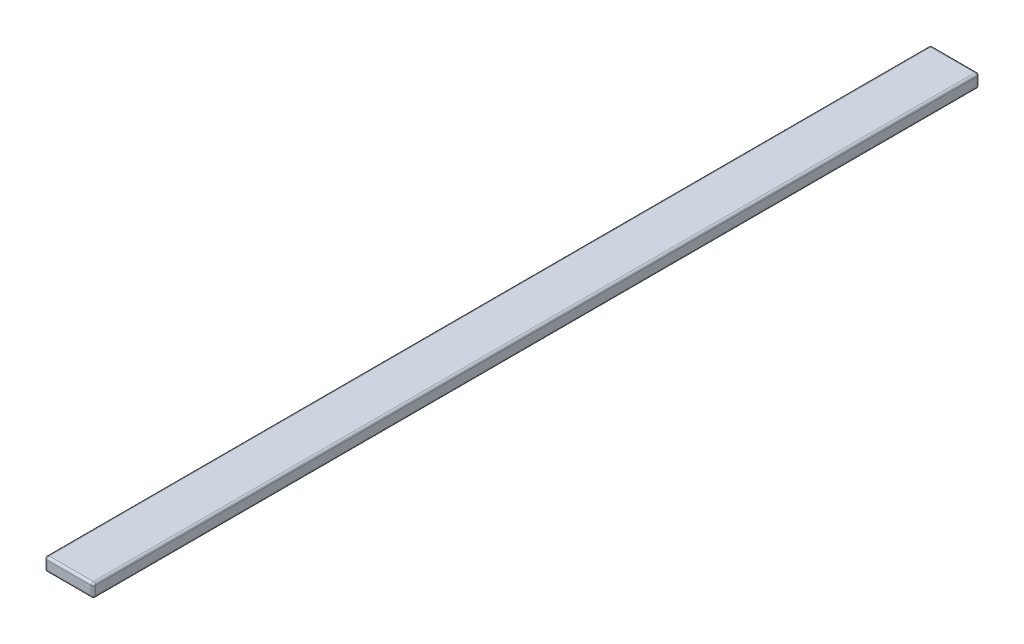
SolidWorks part; units mm, degrees
ref_plane "Front Plane" through (0, 0, 0) normal (0, 0, 1) x (1, 0, 0)
ref_plane "Top Plane" through (0, 0, 0) normal (0, 1, 0) x (1, 0, 0)
ref_plane "Right Plane" through (0, 0, 0) normal (1, 0, 0) x (0, 0, -1)
sketch "Sketch1" plane through (0, 0, 0) normal (0, 0, 1) x (1, 0, 0)
  line L1 (-11, -3) -> (11, -3)
  line L2 (-11, -3) -> (-11, 3)
  line L3 (-11, 3) -> (11, 3)
  line L4 (11, -3) -> (11, 3)
  line L5 (-11, -3) -> (11, 3) construction
  line L6 (-11, 3) -> (11, -3) construction
  point P0 (0, 0)
  dimension "D1" = 22
  dimension "D2" = 6
extrude "Boss-Extrude1" add sketch "Sketch1" along normal blind 400
fillet "Fillet1" radius 1 12 edges at (0, -3, 400) (-11, 0, 400) (0, 3, 400) (11, 0, 400) (0, 3, 0) (-11, 0, 0) (0, -3, 0) (11, 0, 0) (-11, 3, 200) (-11, -3, 200) (11, -3, 200) (11, 3, 200)
sketch "Sketch2" plane through (0, -3, 0) normal (0, -1, 0) x (1, 0, 0)
  line L0 (10, 399) -> (-10, 399) construction
  line L1 (-10, 200) -> (10, 200) construction
  line L2 (-10, 399) -> (-10, 1) construction
  line L3 (10, 1) -> (10, 399) construction
  point P0 (0, 349)
  point P1 (0, 269)
  point P4 (0, 309)
  point P11 (0, 51)
  point P12 (0, 91)
  point P13 (0, 131)
  dimension "D1" = 50
  dimension "D2" = 90
  dimension "D3" = 130
